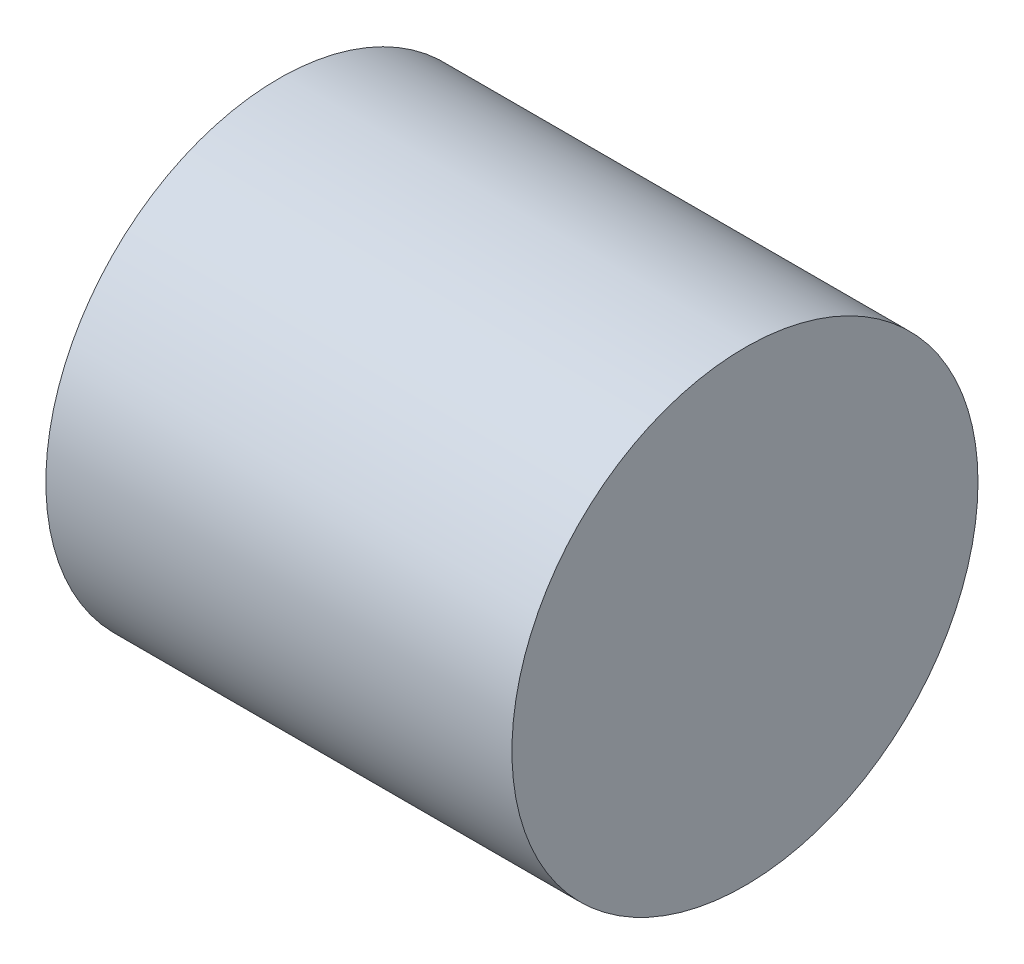
SolidWorks part; units mm, degrees
ref_plane "Front Plane" through (0, 0, 0) normal (0, 0, 1) x (1, 0, 0)
ref_plane "Top Plane" through (0, 0, 0) normal (0, 1, 0) x (1, 0, 0)
ref_plane "Right Plane" through (0, 0, 0) normal (1, 0, 0) x (0, 0, -1)
sketch "Sketch1" plane through (0, 0, 0) normal (1, 0, 0) x (0, 0, -1)
  circle A0 centre (0, 0) radius 0.635
  dimension "D1" = 1.27
extrude "Boss-Extrude1" add sketch "Sketch1" along normal blind 1.27
